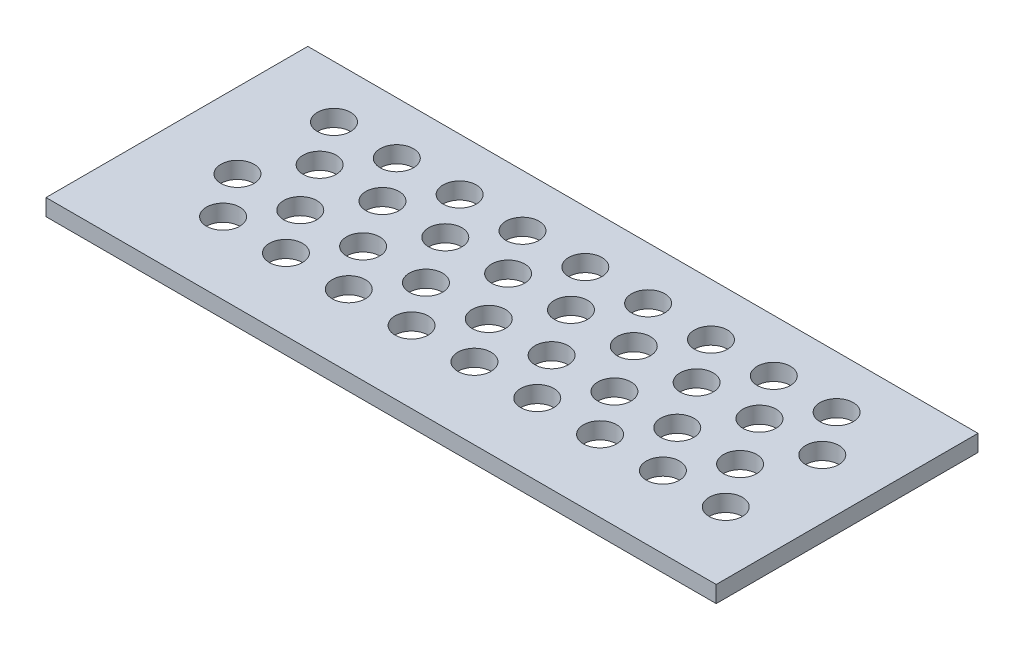
SolidWorks part; units mm, degrees
ref_plane "Front Plane" through (0, 0, 0) normal (0, 0, 1) x (1, 0, 0)
ref_plane "Top Plane" through (0, 0, 0) normal (0, 1, 0) x (1, 0, 0)
ref_plane "Right Plane" through (0, 0, 0) normal (1, 0, 0) x (0, 0, -1)
sketch "Sketch1" plane through (0, 0, 0) normal (0, 1, 0) x (1, 0, 0)
  line L1 (-56.2705, 30.2995) -> (71.7295, 30.2995)
  line L2 (-56.2705, 30.2995) -> (-56.2705, -19.7005)
  line L3 (-56.2705, -19.7005) -> (71.7295, -19.7005)
  line L4 (71.7295, 30.2995) -> (71.7295, -19.7005)
  dimension "D1" = 128
  dimension "D2" = 50
extrude "Boss-Extrude1" add sketch "Sketch1" along normal blind 3.175
sketch "Sketch2" plane through (0, 3.175, 0) normal (0, 1, 0) x (1, 0, 0)
  line L0 (71.7295, 30.2995) -> (-56.2705, 30.2995) construction
  line L1 (-56.2705, 30.2995) -> (-56.2705, -19.7005) construction
  circle A0 centre (-41.2705, 20.2995) radius 3.175
  circle A2 centre (-29.2705, 20.2995) radius 3.175
  circle A3 centre (-17.2705, 20.2995) radius 3.175
  circle A4 centre (-5.2705, 20.2995) radius 3.175
  circle A5 centre (6.7295, 20.2995) radius 3.175
  circle A6 centre (18.7295, 20.2995) radius 3.175
  circle A7 centre (30.7295, 20.2995) radius 3.175
  circle A8 centre (42.7295, 20.2995) radius 3.175
  circle A9 centre (54.7295, 20.2995) radius 3.175
  circle A10 centre (-35.5581, 11.8467) radius 3.175
  circle A11 centre (-23.5581, 11.8467) radius 3.175
  circle A12 centre (-11.5581, 11.8467) radius 3.175
  circle A13 centre (0.4419, 11.8467) radius 3.175
  circle A14 centre (12.4419, 11.8467) radius 3.175
  circle A15 centre (24.4419, 11.8467) radius 3.175
  circle A16 centre (36.4419, 11.8467) radius 3.175
  circle A17 centre (48.4419, 11.8467) radius 3.175
  circle A18 centre (60.4419, 11.8467) radius 3.175
  circle A19 centre (-41.9035, 2.4954) radius 3.175
  circle A20 centre (-29.9035, 2.4954) radius 3.175
  circle A21 centre (-17.9035, 2.4954) radius 3.175
  circle A22 centre (-5.9035, 2.4954) radius 3.175
  circle A23 centre (6.0965, 2.4954) radius 3.175
  circle A24 centre (18.0965, 2.4954) radius 3.175
  circle A25 centre (30.0965, 2.4954) radius 3.175
  circle A26 centre (42.0965, 2.4954) radius 3.175
  circle A27 centre (54.0965, 2.4954) radius 3.175
  circle A28 centre (-36.191, -5.9574) radius 3.175
  circle A29 centre (-24.191, -5.9574) radius 3.175
  circle A30 centre (-12.191, -5.9574) radius 3.175
  circle A31 centre (-0.191, -5.9574) radius 3.175
  circle A32 centre (11.809, -5.9574) radius 3.175
  circle A33 centre (23.809, -5.9574) radius 3.175
  circle A34 centre (35.809, -5.9574) radius 3.175
  circle A35 centre (47.809, -5.9574) radius 3.175
  circle A36 centre (59.809, -5.9574) radius 3.175
  dimension "D1" = 6.35
  dimension "D2" = 9
  dimension "D3" = 10
  dimension "D4" = 15
  dimension "D5" = 6.35
extrude "Cut-Extrude1" cut sketch "Sketch2" against normal blind 3.175
